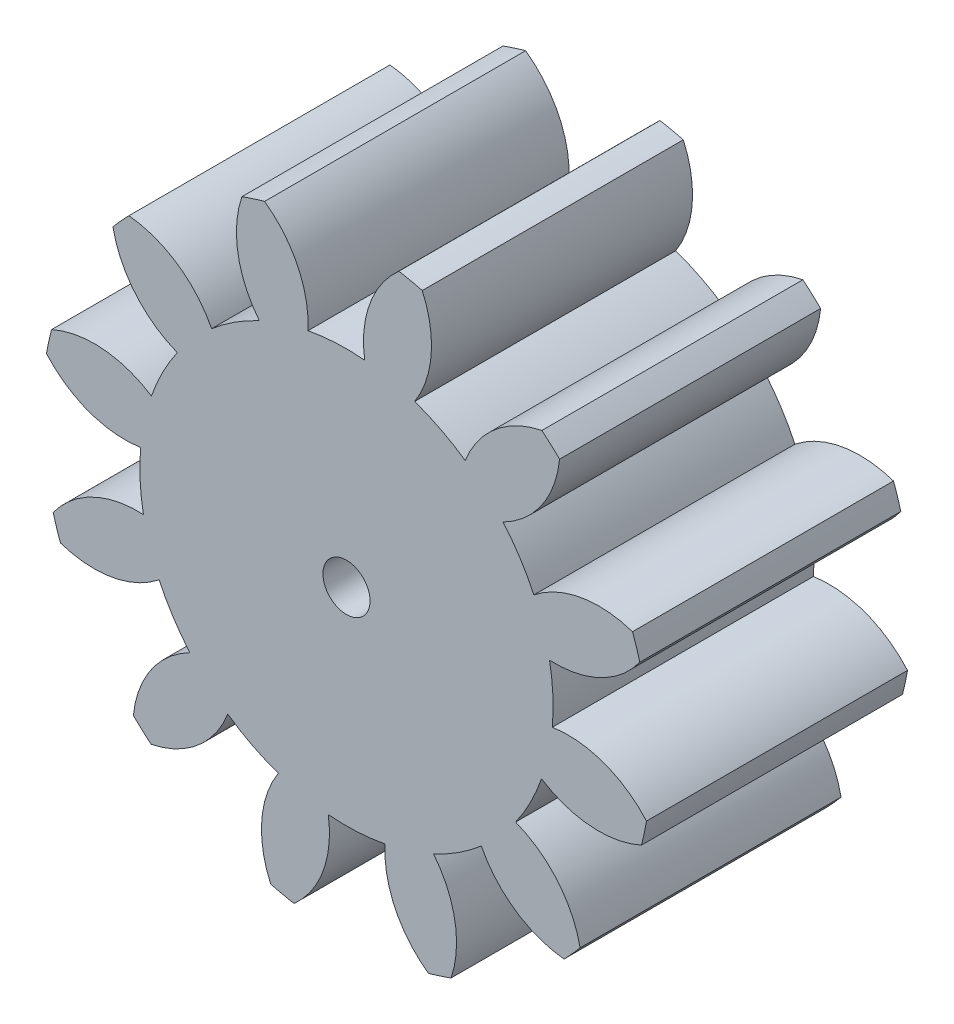
SolidWorks part; units mm, degrees
ref_plane "Front Plane" through (0, 0, 0) normal (0, 0, 1) x (1, 0, 0)
ref_plane "Top Plane" through (0, 0, 0) normal (0, 1, 0) x (1, 0, 0)
ref_plane "Right Plane" through (0, 0, 0) normal (1, 0, 0) x (0, 0, -1)
ref_plane "Plane1" through (0, 0, 0) normal (0, 0, -1) x (-1, 0, 0)
sketch "Sketch1" plane through (0, 0, 0) normal (0, 0, -1) x (-1, 0, 0)
  circle A0 centre (-101.6, 0) radius 0.3969
  arc A1 (-94.2264, -28.7013) -> (-94.9669, -18.9815) centre (-103.4855, -24.5186) ccw
  arc A2 (-94.9669, -18.9815) -> (-90.0505, -16.4591) centre (-101.6, 0) ccw
  arc A3 (-90.0505, -16.4591) -> (-82.5871, -22.7298) centre (-80.5842, -12.7692) ccw
  arc A4 (-82.5871, -22.7298) -> (-80.8636, -21.1693) centre (-101.6, 0) ccw
  arc A5 (-80.8636, -21.1693) -> (-86.3648, -13.1219) centre (-90.9736, -22.1764) ccw
  arc A6 (-86.3648, -13.1219) -> (-83.3683, -8.4792) centre (-101.6, 0) ccw
  arc A7 (-83.3683, -8.4792) -> (-73.7694, -10.1781) centre (-77.0152, -0.5505) ccw
  arc A8 (-73.7694, -10.1781) -> (-73.0571, -7.9649) centre (-101.6, 0) ccw
  arc A9 (-73.0571, -7.9649) -> (-81.845, -3.7463) centre (-81.309, -13.8921) ccw
  arc A10 (-81.845, -3.7463) -> (-81.5712, 1.7726) centre (-101.6, 0) ccw
  arc A11 (-81.5712, 1.7726) -> (-72.409, 5.1008) centre (-80.0337, 11.8156) ccw
  arc A12 (-72.409, 5.1008) -> (-72.8987, 7.3736) centre (-101.6, 0) ccw
  arc A13 (-72.8987, 7.3736) -> (-82.6185, 6.6331) centre (-77.0814, -1.8855) ccw
  arc A14 (-82.6185, 6.6331) -> (-85.1409, 11.5495) centre (-101.6, 0) ccw
  arc A15 (-85.1409, 11.5495) -> (-78.8702, 19.0129) centre (-88.8308, 21.0158) ccw
  arc A16 (-78.8702, 19.0129) -> (-80.4307, 20.7364) centre (-101.6, 0) ccw
  arc A17 (-80.4307, 20.7364) -> (-88.4781, 15.2352) centre (-79.4236, 10.6264) ccw
  arc A18 (-88.4781, 15.2352) -> (-93.1208, 18.2317) centre (-101.6, 0) ccw
  arc A19 (-93.1208, 18.2317) -> (-91.4219, 27.8306) centre (-101.0495, 24.5848) ccw
  arc A20 (-91.4219, 27.8306) -> (-93.6351, 28.5429) centre (-101.6, 0) ccw
  arc A21 (-93.6351, 28.5429) -> (-97.8537, 19.755) centre (-87.7079, 20.291) ccw
  arc A22 (-97.8537, 19.755) -> (-103.3726, 20.0288) centre (-101.6, 0) ccw
  arc A23 (-103.3726, 20.0288) -> (-106.7008, 29.191) centre (-113.4156, 21.5663) ccw
  arc A24 (-106.7008, 29.191) -> (-108.9736, 28.7013) centre (-101.6, 0) ccw
  arc A25 (-108.9736, 28.7013) -> (-108.2331, 18.9815) centre (-99.7145, 24.5186) ccw
  arc A26 (-108.2331, 18.9815) -> (-113.1495, 16.4591) centre (-101.6, 0) ccw
  arc A27 (-113.1495, 16.4591) -> (-120.6129, 22.7298) centre (-122.6158, 12.7692) ccw
  arc A28 (-120.6129, 22.7298) -> (-122.3364, 21.1693) centre (-101.6, 0) ccw
  arc A29 (-122.3364, 21.1693) -> (-116.8352, 13.1219) centre (-112.2264, 22.1764) ccw
  arc A30 (-116.8352, 13.1219) -> (-119.8317, 8.4792) centre (-101.6, 0) ccw
  arc A31 (-119.8317, 8.4792) -> (-129.4306, 10.1781) centre (-126.1848, 0.5505) ccw
  arc A32 (-129.4306, 10.1781) -> (-130.1429, 7.9649) centre (-101.6, 0) ccw
  arc A33 (-130.1429, 7.9649) -> (-121.355, 3.7463) centre (-121.891, 13.8921) ccw
  arc A34 (-121.355, 3.7463) -> (-121.6288, -1.7726) centre (-101.6, 0) ccw
  arc A35 (-121.6288, -1.7726) -> (-130.791, -5.1008) centre (-123.1663, -11.8156) ccw
  arc A36 (-130.791, -5.1008) -> (-130.3013, -7.3736) centre (-101.6, 0) ccw
  arc A37 (-130.3013, -7.3736) -> (-120.5815, -6.6331) centre (-126.1186, 1.8855) ccw
  arc A38 (-120.5815, -6.6331) -> (-118.0591, -11.5495) centre (-101.6, 0) ccw
  arc A39 (-118.0591, -11.5495) -> (-124.3298, -19.0129) centre (-114.3692, -21.0158) ccw
  arc A40 (-124.3298, -19.0129) -> (-122.7693, -20.7364) centre (-101.6, 0) ccw
  arc A41 (-122.7693, -20.7364) -> (-114.7219, -15.2352) centre (-123.7764, -10.6264) ccw
  arc A42 (-114.7219, -15.2352) -> (-110.0792, -18.2317) centre (-101.6, 0) ccw
  arc A43 (-110.0792, -18.2317) -> (-111.7781, -27.8306) centre (-102.1505, -24.5848) ccw
  arc A44 (-111.7781, -27.8306) -> (-109.5649, -28.5429) centre (-101.6, 0) ccw
  arc A45 (-109.5649, -28.5429) -> (-105.3463, -19.755) centre (-115.4921, -20.291) ccw
  arc A46 (-105.3463, -19.755) -> (-99.8274, -20.0288) centre (-101.6, 0) ccw
  arc A47 (-99.8274, -20.0288) -> (-96.4992, -29.191) centre (-89.7844, -21.5663) ccw
  arc A48 (-96.4992, -29.191) -> (-94.2264, -28.7013) centre (-101.6, 0) ccw
extrude "Boss-Extrude1" add sketch "Sketch1" against normal blind 25.4
sketch "Sketch3" plane through (0, 0, 25.4) normal (0, 0, 1) x (1, 0, 0)
  circle A0 centre (101.6, 0) radius 2.2923
  dimension "D1" = 4.5847
extrude "Cut-Extrude1" cut sketch "Sketch3" against normal blind 45.3009
